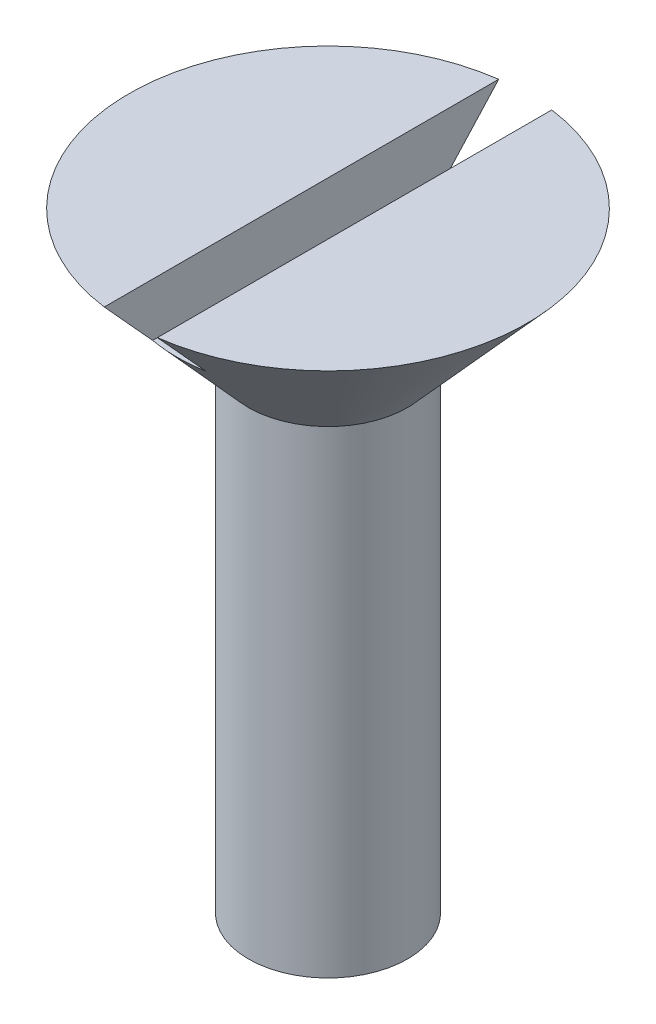
SolidWorks part; units mm, degrees
ref_plane "Front Plane" through (0, 0, 0) normal (0, 0, 1) x (1, 0, 0)
ref_plane "Top Plane" through (0, 0, 0) normal (0, 1, 0) x (1, 0, 0)
ref_plane "Right Plane" through (0, 0, 0) normal (1, 0, 0) x (0, 0, -1)
sketch "Sketch1" plane through (0, 0, 0) normal (0, 0, 1) x (1, 0, 0)
  line L0 (0, 0) -> (3, 1.7321)
  line L1 (3, 1.7321) -> (3, 19.7321)
  line L2 (3, 19.7321) -> (7.5, 24.7321)
  line L3 (7.5, 24.7321) -> (0, 24.7321)
  line L4 (0, 24.7321) -> (0, 0)
  point P3 (0, 0)
  dimension "D1" = 18
  dimension "D2" = 120
  dimension "D3" = 3
  dimension "D4" = 7.5
  dimension "D5" = 5
revolve "Revolve1" add sketch "Sketch1" angle 360 about L4
sketch "Sketch2" plane through (0, 0, 0) normal (0, 0, 1) x (1, 0, 0)
  line L0 (7.5, 24.7321) -> (-7.5, 24.7321) construction
  line L1 (-1, 22.7321) -> (1, 22.7321)
  line L2 (-1, 22.7321) -> (-1, 26.7321)
  line L3 (-1, 26.7321) -> (1, 26.7321)
  line L4 (1, 22.7321) -> (1, 26.7321)
  line L5 (-1, 22.7321) -> (1, 26.7321) construction
  line L6 (-1, 26.7321) -> (1, 22.7321) construction
  point P0 (0, 24.7321)
  dimension "D1" = 2
  dimension "D2" = 4
extrude "Cut-Extrude1" cut sketch "Sketch2" against normal through all both and the other way through all
